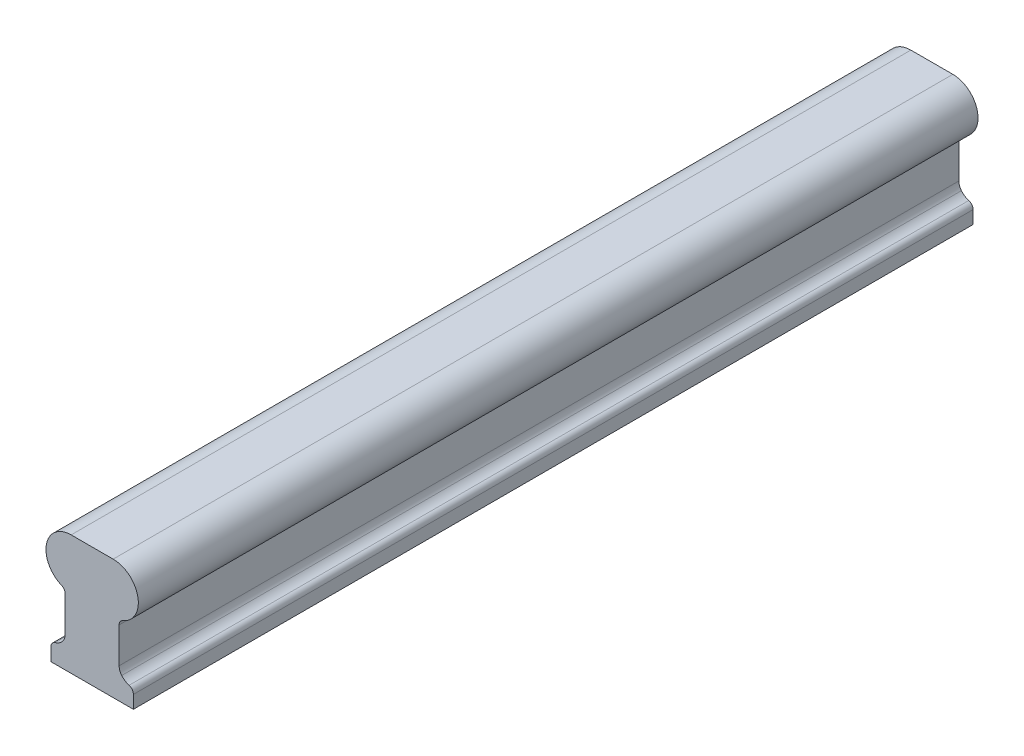
SolidWorks part; units mm, degrees
ref_plane "Front" through (0, 0, 0) normal (0, 0, 1) x (1, 0, 0)
ref_plane "Top" through (0, 0, 0) normal (0, 1, 0) x (1, 0, 0)
ref_plane "Right" through (0, 0, 0) normal (1, 0, 0) x (0, 0, -1)
sketch "Sketch1" plane through (0, 0, 0) normal (0, 0, 1) x (1, 0, 0)
  line L0 (17.4625, 0) -> (17.4625, 57.9454) construction
  line L1 (0, 0) -> (34.925, 0)
  line L2 (6.0325, 27.94) -> (6.0325, 12.9561)
  line L3 (8.5725, 50.8) -> (26.3525, 50.8)
  line L4 (28.8925, 27.94) -> (28.8925, 12.9561)
  line L5 (0, 0) -> (0, 5.4701)
  line L6 (34.925, 0) -> (34.925, 5.4701)
  arc A0 (8.5725, 50.8) -> (4.4694, 30.2846) centre (8.5725, 40.132) ccw
  arc A1 (26.3525, 50.8) -> (30.4556, 30.2846) centre (26.3525, 40.132) cw
  arc A2 (6.0325, 12.9561) -> (4.9372, 9.9462) centre (1.3493, 12.9561) cw
  arc A3 (28.8925, 12.9561) -> (29.9878, 9.9462) centre (33.5757, 12.9561) ccw
  arc A4 (1.8219, 7.9065) -> (4.9372, 9.9462) centre (0, 14.088) ccw
  arc A5 (33.1031, 7.9065) -> (29.9878, 9.9462) centre (34.925, 14.088) cw
  arc A6 (33.1031, 7.9065) -> (34.925, 5.4701) centre (32.385, 5.4701) cw
  arc A7 (0, 5.4701) -> (1.8219, 7.9065) centre (2.54, 5.4701) cw
  arc A8 (28.8925, 27.94) -> (30.4556, 30.2846) centre (31.4325, 27.94) cw
  arc A9 (4.4694, 30.2846) -> (6.0325, 27.94) centre (3.4925, 27.94) cw
  dimension "D1" = 2.54
  dimension "D2" = 2.54
  dimension "D6" = 10.668
  dimension "D7" = 10.668
  dimension "D3" = 22.86
  dimension "D4" = 50.8
  dimension "D5" = 17.78
  dimension "D8" = 34.925
  dimension "D9" = 27.94
extrude "Base-Extrude" add sketch "Sketch1" along normal blind 355.6
